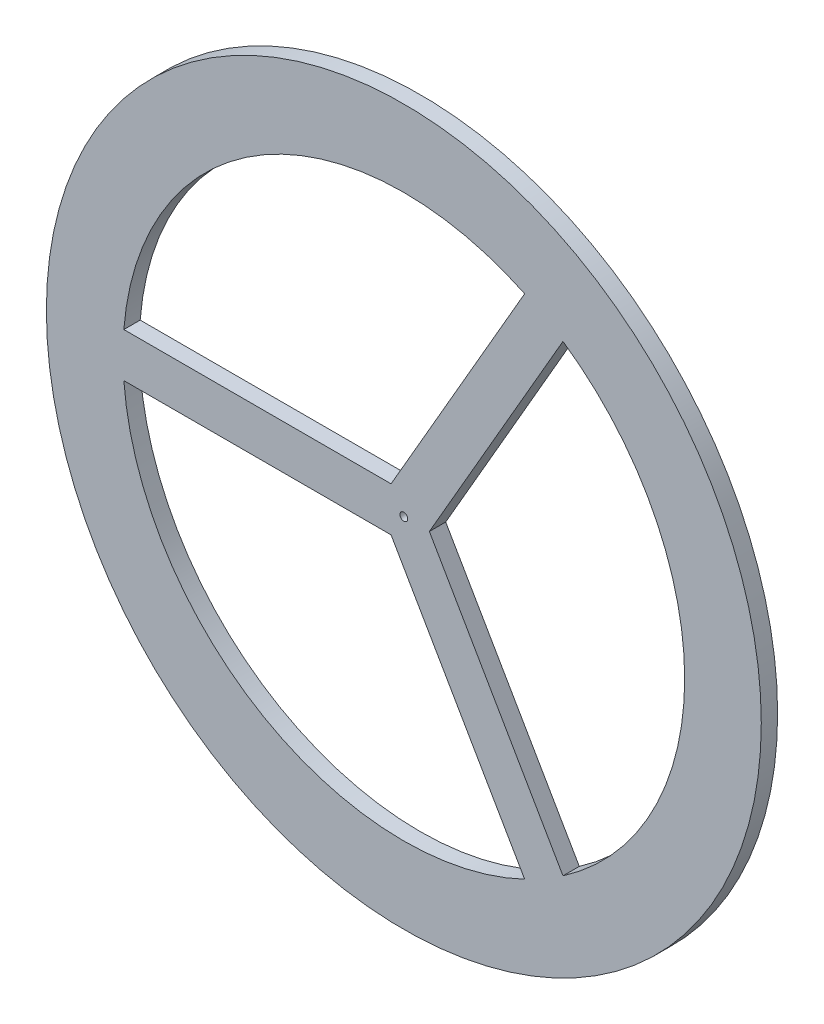
SolidWorks part; units mm, degrees
material "Acrylic (Medium-high impact)"
ref_plane "Front Plane" through (0, 0, 0) normal (0, 0, 1) x (1, 0, 0)
ref_plane "Top Plane" through (0, 0, 0) normal (0, 1, 0) x (1, 0, 0)
ref_plane "Right Plane" through (0, 0, 0) normal (1, 0, 0) x (0, 0, -1)
sketch "Sketch1" plane through (0, 0, 0) normal (0, 0, 1) x (1, 0, 0)
  line L1 (12.5, 0) -> (-6.25, 10.8253) construction
  line L2 (-6.25, 10.8253) -> (-6.25, -10.8253) construction
  line L3 (-6.25, -10.8253) -> (12.5, 0) construction
  line L4 (0, 0) -> (-137.5, 0) construction
  line L5 (-6.25, 10.8253) -> (-137.0732, 10.8253)
  line L6 (-6.25, -10.8253) -> (-137.0732, -10.8253)
  line L7 (12.5, 0) -> (77.9116, 113.2962)
  line L8 (-6.25, 10.8253) -> (59.1616, 124.1215)
  line L9 (-6.25, -10.8253) -> (59.1616, -124.1215)
  line L10 (12.5, 0) -> (77.9116, -113.2962)
  circle A0 centre (0, 0) radius 175
  arc A1 (-137.0732, -10.8253) -> (59.1616, -124.1215) centre (0, 0) ccw
  circle A2 centre (0, 0) radius 12.5 construction
  arc A3 (59.1616, 124.1215) -> (-137.0732, 10.8253) centre (0, 0) ccw
  arc A4 (77.9116, -113.2962) -> (77.9116, 113.2962) centre (0, 0) ccw
  circle A5 centre (0, 0) radius 137.5 construction
  point P24 (0, 0)
  dimension "D1" = 350
  dimension "D2" = 275
  dimension "D3" = 25
  dimension "D4" = 275
  dimension "D6" = 3
extrude "Boss-Extrude1" add sketch "Sketch1" along normal blind 8
sketch "Sketch2" plane through (0, 0, 0) normal (0, 0, 1) x (1, 0, 0)
  circle A0 centre (0, 0) radius 1.9
  dimension "D1" = 3.8
extrude "Cut-Extrude2" cut sketch "Sketch2" against normal through all and the other way through all
